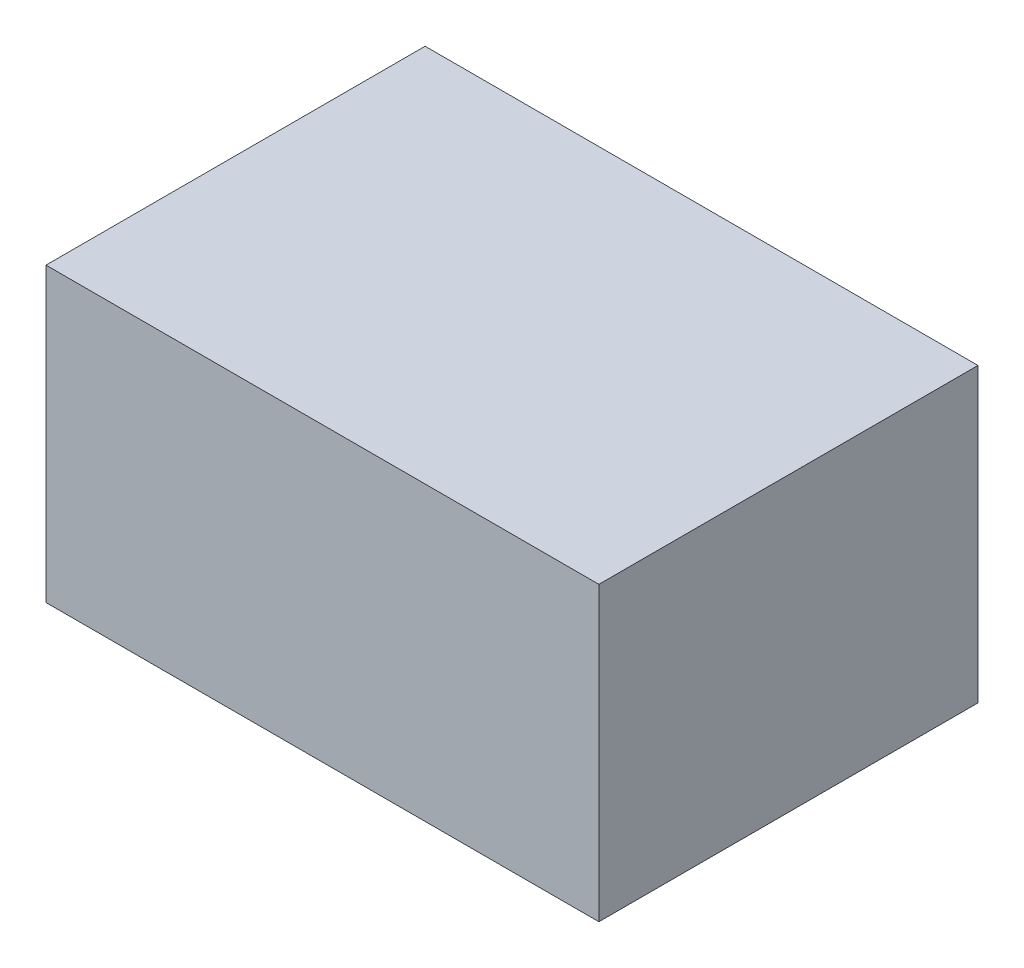
SolidWorks part; units mm, degrees
ref_plane "前视基准面" through (0, 0, 0) normal (0, 0, 1) x (1, 0, 0)
ref_plane "上视基准面" through (0, 0, 0) normal (0, 1, 0) x (1, 0, 0)
ref_plane "右视基准面" through (0, 0, 0) normal (1, 0, 0) x (0, 0, -1)
sketch "草图1" plane through (0, 0, 0) normal (0, 0, 1) x (1, 0, 0)
  line L0 (46.7152, 23.0462) -> (46.7152, 4.5462)
  line L1 (46.7152, 4.5462) -> (11.7152, 4.5462)
  line L2 (11.7152, 4.5462) -> (11.7152, 23.0462)
  line L3 (11.7152, 23.0462) -> (46.7152, 23.0462)
  dimension "D1" = 18.5
  dimension "D2" = 35
extrude "凸台-拉伸1" add sketch "草图1" along normal blind 24
